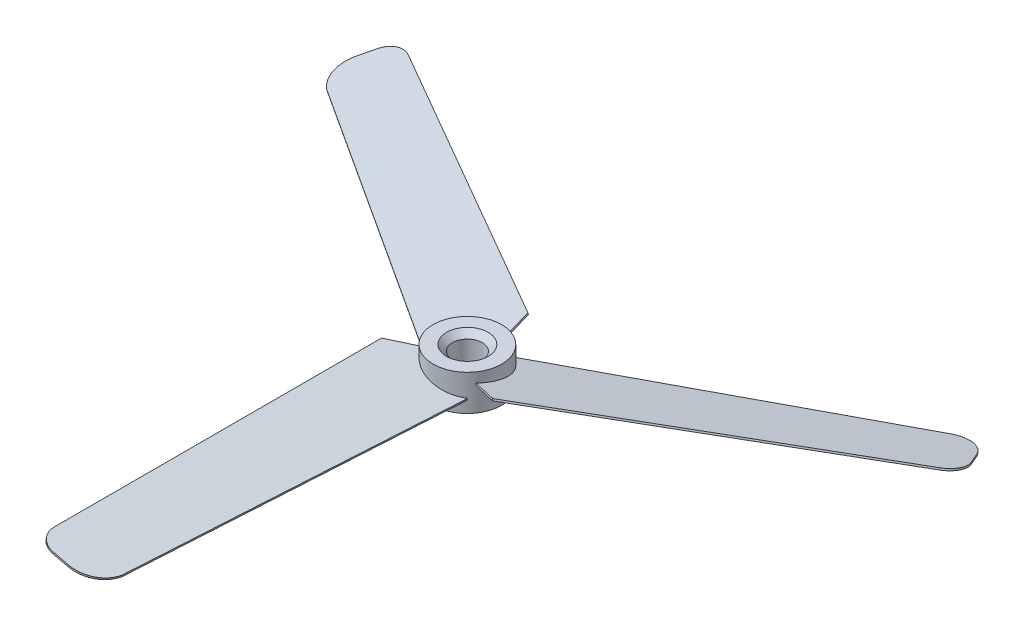
SolidWorks part; units mm, degrees
ref_plane "Front Plane" through (0, 0, 0) normal (0, 0, 1) x (1, 0, 0)
ref_plane "Top Plane" through (0, 0, 0) normal (0, 1, 0) x (1, 0, 0)
ref_plane "Right Plane" through (0, 0, 0) normal (1, 0, 0) x (0, 0, -1)
sketch "Sketch2" plane through (0, 0, 0) normal (0, 1, 0) x (1, 0, 0)
  circle A0 centre (0, 0) radius 5.75
  dimension "D1" = 11.5
extrude "Boss-Extrude3" add sketch "Sketch2" along normal mid plane 6 contours A0
sketch "Sketch6" plane through (0, 0, 0) normal (0, 0, 1) x (1, 0, 0)
  line L0 (-5.75, 1.3275) -> (5.75, -1.3275) construction
  line L2 (-5.75, 3) -> (-5.75, -3) construction
  line L3 (5.75, -3) -> (5.75, 3) construction
  line L4 (-5.75, -3) -> (5.75, -3) construction
  dimension "D1" = 13
ref_plane "Plane1" through (0, 0, 0) normal (-0.225, -0.9744, 0) x (0.9744, -0.225, 0)
sketch "Sketch7" plane through (0, 0, 0) normal (-0.225, -0.9744, 0) x (0.9744, -0.225, 0)
  line L0 (-4.6187, 1.8835) -> (-9.1818, 5.4982)
  line L1 (-9.1818, 5.4982) -> (-9.1818, 60.5)
  line L2 (-6.1818, 63.5) -> (-3.5291, 63.5)
  arc A0 (1.402, 59.3273) -> (-3.5291, 63.5) centre (-3.5291, 58.5) ccw
  arc A1 (-9.1818, 60.5) -> (-6.1818, 63.5) centre (-6.1818, 60.5) cw
  ellipse E0 centre (0.6749, 0) end of major axis (0.6749, 5.75) minor radius 5.6026 construction
  spline S0 degree 2 poles (-4.6187, 1.8835) (-0.2122, 8.9389) (4.254, 2.2281) knots 0 0 0 1 1 1
  spline S1 degree 1 poles (1.402, 59.3273) (4.254, 2.2281) knots 0 0 1 1
  point P7 (0, 0)
  point P9 (0, 0)
  point P10 (0, 0)
  dimension "D2" = 5
  dimension "D3" = 3
  dimension "D1" = 63.5
extrude "Boss-Extrude4" add sketch "Sketch7" along normal mid plane 0.3
extrude "Cut-Extrude2" cut sketch "Sketch10" against normal through all contours A0
sketch "Sketch10" plane through (0, -3, 0) normal (0, -1, 0) x (1, 0, 0)
  circle A0 centre (0, 0) radius 2.5
pattern_circular "CirPattern1" count 3 over 360 about axis through (0, 0, 0) along (0, 1, 0) of "Boss-Extrude4"
chamfer "Chamfer1" distance 1 angle 45 2 edges at (0, -3, -2.5) (0, 3, -2.5)
